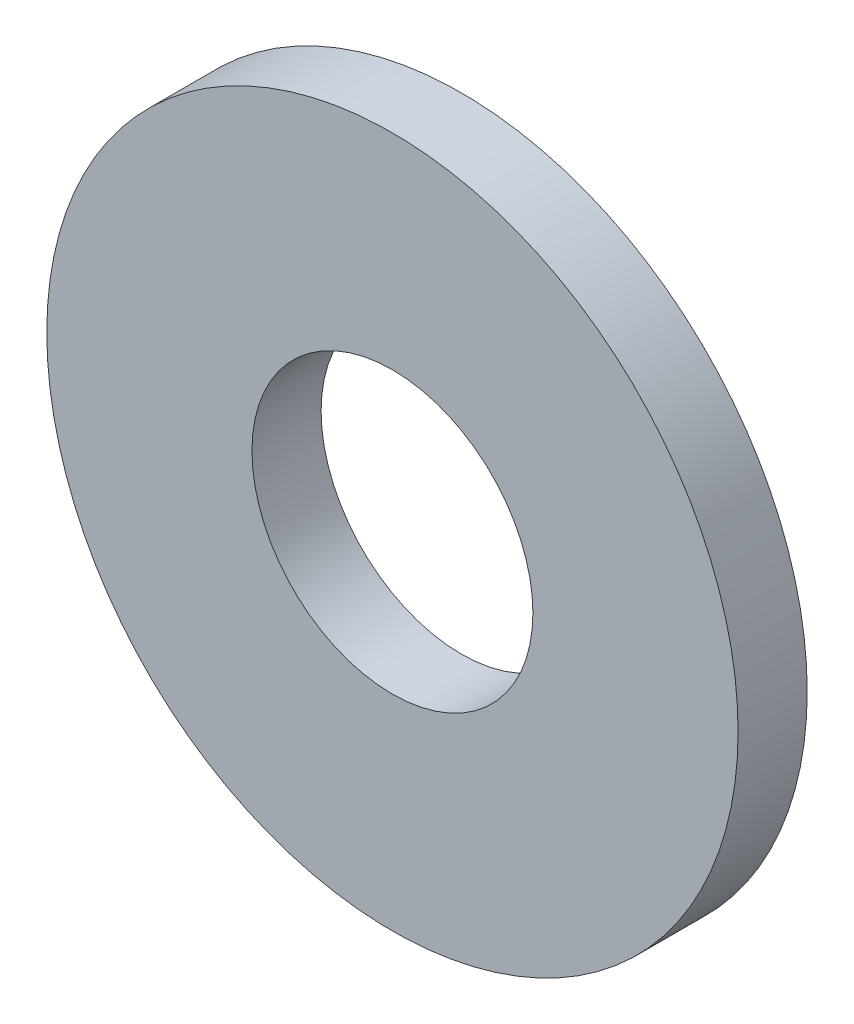
SolidWorks part; units mm, degrees
material "Brass"
ref_plane "Front Plane" through (0, 0, 0) normal (0, 0, 1) x (1, 0, 0)
ref_plane "Top Plane" through (0, 0, 0) normal (0, 1, 0) x (1, 0, 0)
ref_plane "Right Plane" through (0, 0, 0) normal (1, 0, 0) x (0, 0, -1)
sketch "Sketch1" plane through (0, 0, 0) normal (0, 0, 1) x (1, 0, 0)
  circle A0 centre (0, 0) radius 7.9375
  circle A1 centre (0, 0) radius 3.2258
  dimension "D1" = 15.875
  dimension "ID" = 6.4516
extrude "Extrude1" add sketch "Sketch1" along normal mid plane 1.5875
sketch "Sketch2" plane through (0, 0, 0) normal (1, 0, 0) x (0, 0, -1)
  line L0 (-0.7937, -3.2258) -> (0.7937, -3.2258) construction
  line L3 (0.7937, 3.2258) -> (-0.7937, 3.2258) construction
  line L5 (-0.7937, -3.2258) -> (0.7937, -3.2258)
  line L6 (0.7937, 3.2258) -> (-0.7937, 3.2258)
sketch "Sketch4" plane through (0, 0, 0.7937) normal (0, 0, 1) x (1, 0, 0)
  line L0 (0, 0) -> (-2.281, 2.281)
  line L1 (0, -0.8731) -> (0, 0.8731) construction
  circle A0 centre (0, 0) radius 3.2258 construction
  dimension "D1" = 45
